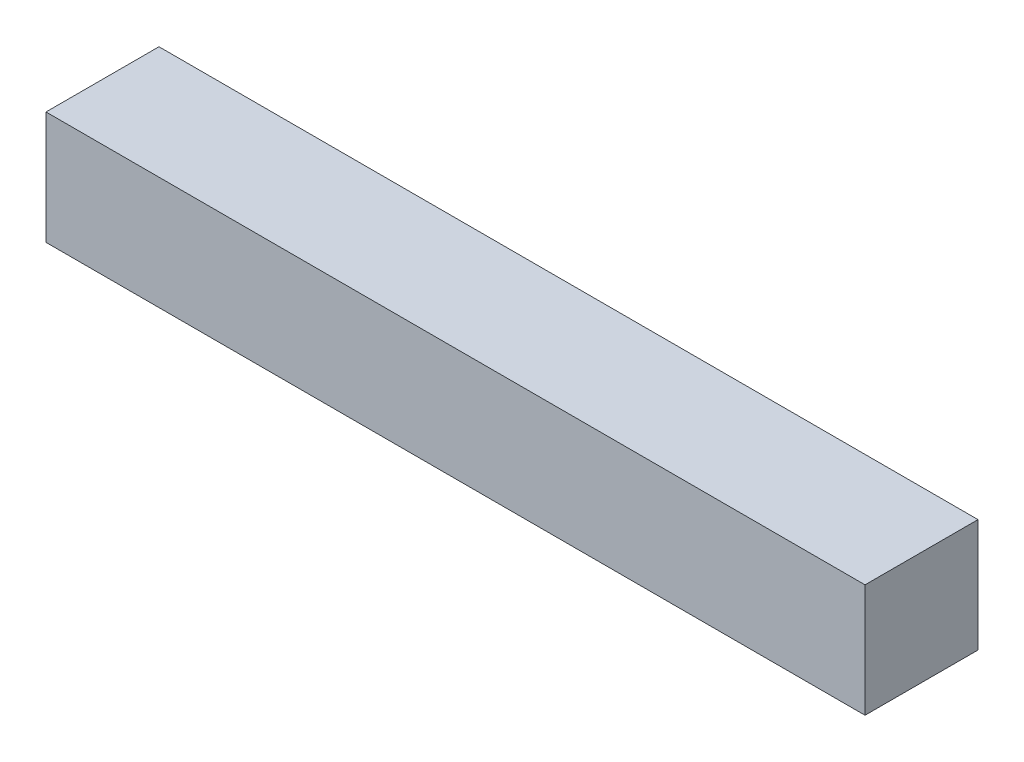
SolidWorks part; units mm, degrees
ref_plane "Front Plane" through (0, 0, 0) normal (0, 0, 1) x (1, 0, 0)
ref_plane "Top Plane" through (0, 0, 0) normal (0, 1, 0) x (1, 0, 0)
ref_plane "Right Plane" through (0, 0, 0) normal (1, 0, 0) x (0, 0, -1)
sketch "Sketch1" plane through (0, 0, 0) normal (0, 0, 1) x (1, 0, 0)
  line L1 (0, 0) -> (14.5, 0)
  line L2 (0, 0) -> (0, 2)
  line L3 (0, 2) -> (14.5, 2)
  line L4 (14.5, 0) -> (14.5, 2)
  dimension "D1" = 14.5
  dimension "D2" = 2
extrude "Boss-Extrude1" add sketch "Sketch1" along normal blind 2
